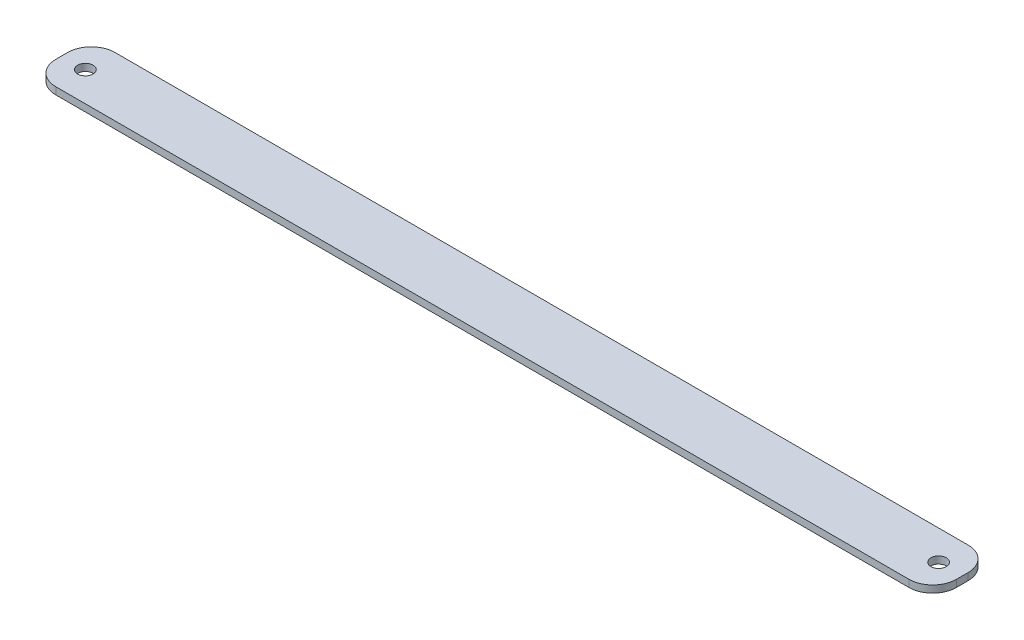
SolidWorks part; units mm, degrees
material "ASTM A36 Steel"
ref_plane "Front Plane" through (0, 0, 0) normal (0, 0, 1) x (1, 0, 0)
ref_plane "Top Plane" through (0, 0, 0) normal (0, 1, 0) x (1, 0, 0)
ref_plane "Right Plane" through (0, 0, 0) normal (1, 0, 0) x (0, 0, -1)
sketch "Sketch1" plane through (0, 0, 0) normal (0, 1, 0) x (1, 0, 0)
  line L1 (-180, 12.5) -> (180, 12.5)
  line L2 (-190, 2.5) -> (-190, -2.5)
  line L3 (-180, -12.5) -> (180, -12.5)
  line L4 (190, 2.5) -> (190, -2.5)
  line L5 (-190, 12.5) -> (190, -12.5) construction
  line L6 (-190, -12.5) -> (190, 12.5) construction
  arc A0 (180, -12.5) -> (190, -2.5) centre (180, -2.5) ccw
  arc A1 (190, 2.5) -> (180, 12.5) centre (180, 2.5) ccw
  arc A2 (-180, -12.5) -> (-190, -2.5) centre (-180, -2.5) cw
  arc A3 (-180, 12.5) -> (-190, 2.5) centre (-180, 2.5) ccw
  circle A4 centre (-180, 0) radius 3.25
  circle A5 centre (180, 0) radius 3.25
  point P0 (0, 0)
  dimension "D3" = 10
  dimension "D4" = 6.5
  dimension "D5" = 6.5
  dimension "D1" = 25
  dimension "D2" = 380
extrude "Boss-Extrude1" add sketch "Sketch1" along normal blind 3
